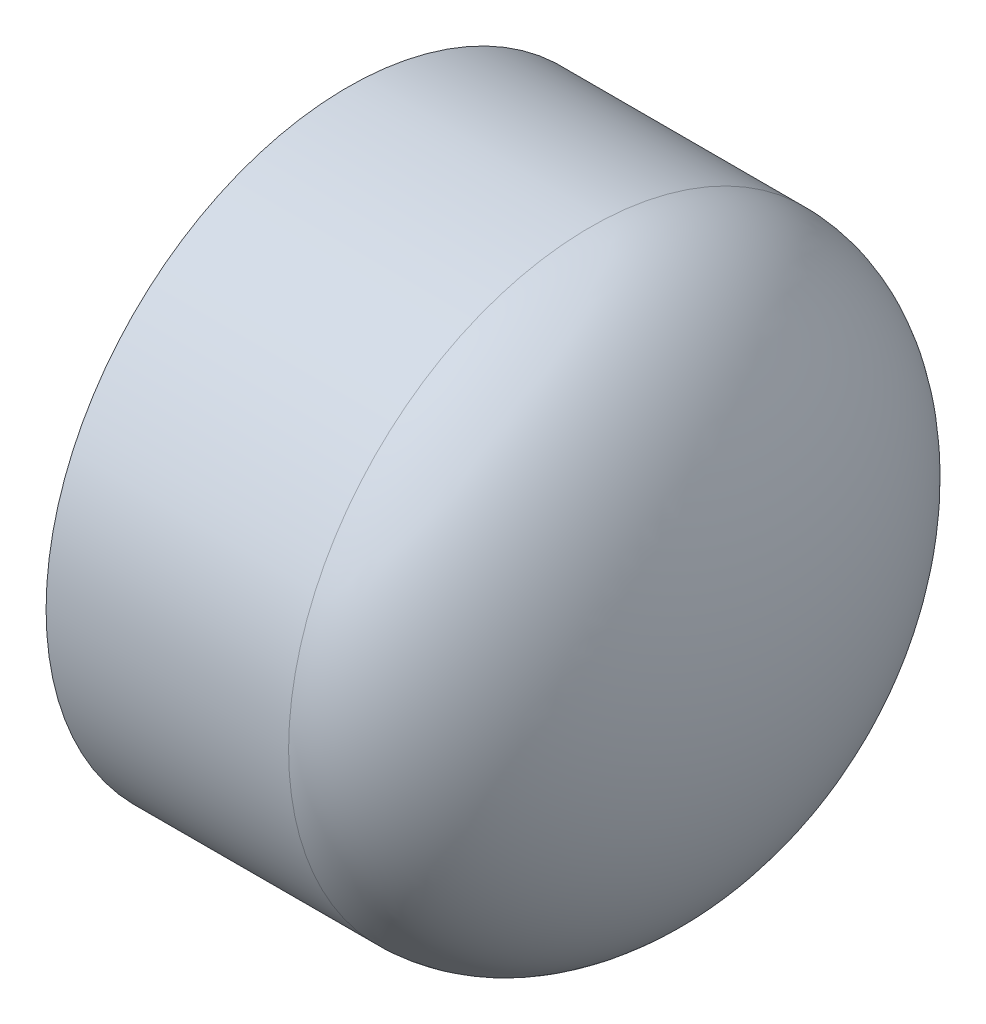
SolidWorks part; units mm, degrees
material "PVC Rigid"
ref_plane "Front Plane" through (0, 0, 0) normal (0, 0, 1) x (1, 0, 0)
ref_plane "Top Plane" through (0, 0, 0) normal (0, 1, 0) x (1, 0, 0)
ref_plane "Right Plane" through (0, 0, 0) normal (1, 0, 0) x (0, 0, -1)
sketch "Sketch0" plane through (0, 0, 0) normal (0, 0, 1) x (1, 0, 0)
  line L3 (-44.3992, 0) -> (44.3992, 0) construction
  line L4 (-44.3992, 63.8175) -> (-44.3992, -63.8175) construction
  line L5 (6.9088, 57.0357) -> (-44.3992, 57.3786) construction
  line L6 (6.9088, 57.0357) -> (6.9088, -57.0357) construction
  line L7 (6.9088, -57.0357) -> (-44.3992, -57.3786) construction
  line L8 (-44.3992, 57.3786) -> (-44.3992, -57.3786) construction
  line L14 (6.9088, 51.1302) -> (6.9088, -51.1302) construction
  point P0 (6.9088, 0)
  dimension "H" = 37.4904
  dimension "M" = 127.635
  dimension "OD A" = 114.7572
  dimension "OD B" = 114.0714
  dimension "ID" = 102.2604
  dimension "L" = 88.7984
  dimension "C" = 51.308
sketch "Sketch1" plane through (0, 0, 0) normal (0, 0, 1) x (1, 0, 0)
  line L1 (-44.3992, 0) -> (44.3992, 0) construction
  line L2 (-44.3992, 0) -> (44.3992, 0) construction
  line L3 (37.6174, 0) -> (44.3992, 0)
  line L4 (-44.3992, -63.8175) -> (-44.3992, -57.3786)
  line L5 (-44.3992, -57.3786) -> (6.9088, -57.0357)
  line L6 (6.9088, -57.0357) -> (6.9088, -63.8175) construction
  line L9 (6.9088, -63.8175) -> (-44.3992, -63.8175)
  ellipse E2 centre (6.9088, 0) end of major axis (6.9088, 63.8175) minor radius 37.4904 (6.9088, -63.8175) -> (44.3992, 0) ccw
  ellipse E3 centre (6.9088, 0) end of major axis (6.9088, -57.0357) minor radius 30.7086 (6.9088, -57.0357) -> (37.6174, 0) ccw
revolve "Revolve1" add sketch "Sketch1" angle 360 about L1
